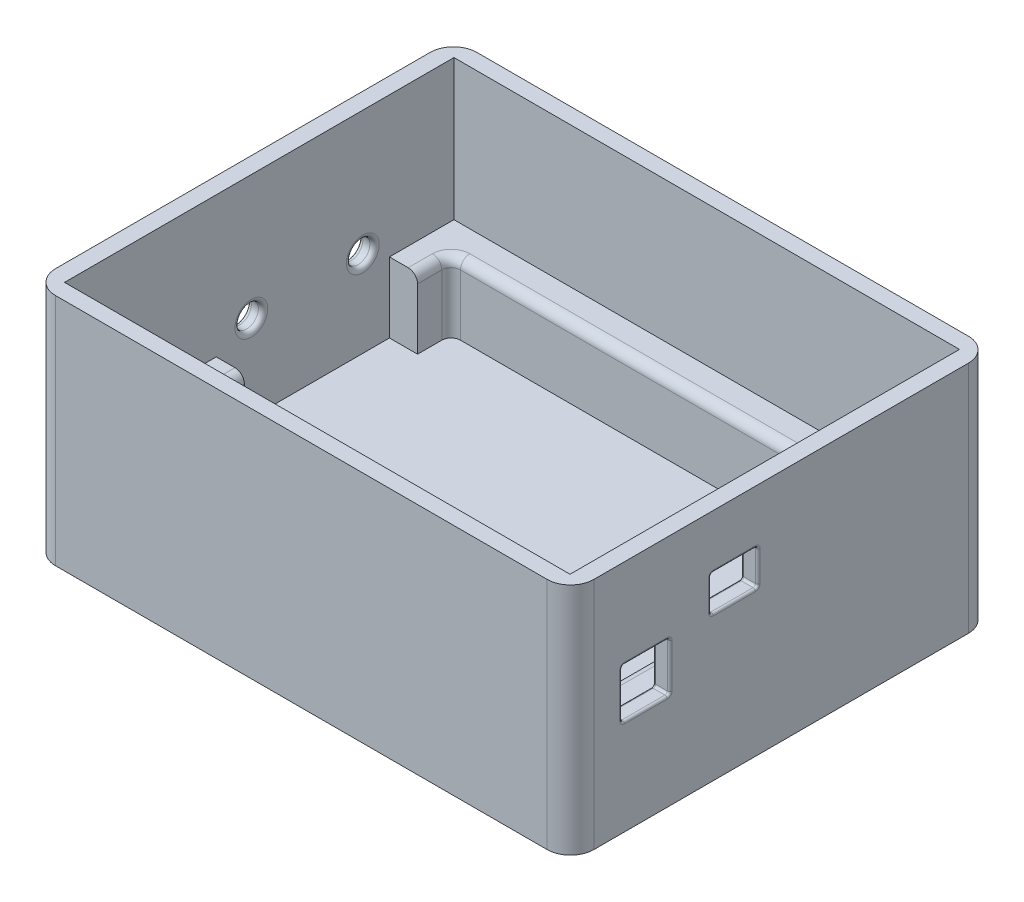
SolidWorks part; units mm, degrees
ref_plane "Front Plane" through (0, 0, 0) normal (0, 0, 1) x (1, 0, 0)
ref_plane "Top Plane" through (0, 0, 0) normal (0, 1, 0) x (1, 0, 0)
ref_plane "Right Plane" through (0, 0, 0) normal (1, 0, 0) x (0, 0, -1)
sketch "Sketch2" plane through (0, 0, 0) normal (0, 1, 0) x (1, 0, 0)
  line L1 (-57.5, 45) -> (57.5, 45)
  line L2 (-57.5, 45) -> (-57.5, -45)
  line L3 (-57.5, -45) -> (57.5, -45)
  line L4 (57.5, 45) -> (57.5, -45)
  line L5 (-57.5, 45) -> (57.5, -45) construction
  line L6 (-57.5, -45) -> (57.5, 45) construction
  point P0 (0, 0)
  dimension "D1" = 115
  dimension "D2" = 90
extrude "Boss-Extrude1" add sketch "Sketch2" along normal blind 50
fillet "Fillet1" radius 5 4 edges at (57.5, 25, 45) (-57.5, 25, 45) (-57.5, 25, -45) (57.5, 25, -45)
sketch "Sketch3" plane through (0, 50, 0) normal (0, 1, 0) x (1, 0, 0)
  line L1 (-54, 41.6) -> (54, 41.6)
  line L2 (-54, 41.6) -> (-54, -41.6)
  line L3 (-54, -41.6) -> (54, -41.6)
  line L4 (54, 41.6) -> (54, -41.6)
  line L5 (-54, 41.6) -> (54, -41.6) construction
  line L6 (-54, -41.6) -> (54, 41.6) construction
  point P0 (0, 0)
  dimension "D1" = 108
  dimension "D2" = 83.2
extrude "Cut-Extrude1" cut sketch "Sketch3" against normal blind 30
sketch "Sketch4" plane through (0, 20, 0) normal (0, 1, 0) x (1, 0, 0)
  line L1 (-48, 35) -> (48, 35)
  line L2 (-48, 35) -> (-48, -35)
  line L3 (-48, -35) -> (48, -35)
  line L4 (48, 35) -> (48, -35)
  line L5 (-48, 35) -> (48, -35) construction
  line L6 (-48, -35) -> (48, 35) construction
  point P0 (0, 0)
  dimension "D1" = 96
  dimension "D2" = 70
extrude "Cut-Extrude2" cut sketch "Sketch4" against normal blind 15
fillet "Fillet2" radius 2 8 edges at (0, 20, 35) (48, 12.5, 35) (-48, 12.5, 35) (-48, 20, 0) (-48, 12.5, -35) (48, 20, 0) (0, 20, -35) (48, 12.5, -35)
sketch "Sketch5" plane through (0, 20, 0) normal (0, 1, 0) x (1, 0, 0)
  line L0 (-54, 41.6) -> (-54, -41.6) construction
  line L1 (-54, 27.8195) -> (-48, 27.8195)
  line L2 (-54, 27.8195) -> (-54, -9.1811)
  line L3 (-54, -9.1811) -> (-48, -9.1811)
  line L4 (-48, 27.8195) -> (-48, -9.1811)
  line L5 (-48, 33) -> (-48, -33) construction
extrude "Cut-Extrude3" cut sketch "Sketch5" against normal blind 15
sketch "Sketch7" plane through (0, 20, 0) normal (0, 1, 0) x (1, 0, 0)
  line L0 (54, -41.6) -> (54, 41.6) construction
  line L1 (54, 33.204) -> (48, 33.204)
  line L2 (54, 33.204) -> (54, 7.8005)
  line L3 (54, 7.8005) -> (48, 7.8005)
  line L4 (48, 33.204) -> (48, 7.8005)
  line L5 (48, -33) -> (48, 33) construction
extrude "Cut-Extrude5" cut sketch "Sketch7" against normal blind 15
sketch "Sketch8" plane through (-54, 0, 0) normal (1, 0, 0) x (0, 0, -1)
  line L0 (41.585, 20.4115) -> (-41.6, 20.4115) construction
  circle A0 centre (22.1259, 23.4115) radius 2.5
  circle A1 centre (-1.6908, 23.4115) radius 2.5
  dimension "D1" = 5
  dimension "D2" = 5
  dimension "D3" = 3
  dimension "D4" = 3
extrude "Cut-Extrude6" cut sketch "Sketch8" against normal blind 10
fillet "Fillet3" radius 1 4 edges at (-57.5, 23.4115, -24.6259) (-57.5, 23.4115, -0.8092) (-54, 23.4115, -0.8092) (-54, 23.4115, -24.6259)
sketch "Sketch9" plane through (54, 0, 0) normal (-1, 0, 0) x (0, 0, 1)
  line L1 (23.82, 30.9115) -> (33.98, 30.9115)
  line L2 (23.82, 30.9115) -> (23.82, 20.5115)
  line L3 (23.82, 20.5115) -> (33.98, 20.5115)
  line L4 (33.98, 30.9115) -> (33.98, 20.5115)
extrude "Cut-Extrude7" cut sketch "Sketch9" against normal blind 10
fillet "Fillet9" radius 0.5 12 edges at (57.5, 25.7115, 33.98) (54, 25.7115, 33.98) (57.5, 30.9115, 28.9) (54, 30.9115, 28.9) (55.75, 30.9115, 33.98) (57.5, 20.5115, 28.9) (55.75, 20.5115, 33.98) (54, 20.5115, 28.9) (57.5, 25.7115, 23.82) (55.75, 20.5115, 23.82) (54, 25.7115, 23.82) (55.75, 30.9115, 23.82)
sketch "Sketch10" plane through (57.5, 0, 0) normal (1, 0, 0) x (0, 0, -1)
  line L0 (-40, 50) -> (-40, 0) construction
  line L1 (-15, 38.4754) -> (-5, 38.4754)
  line L2 (-15, 38.4754) -> (-15, 30.9754)
  line L3 (-15, 30.9754) -> (-5, 30.9754)
  line L4 (-5, 38.4754) -> (-5, 30.9754)
  dimension "D1" = 10
  dimension "D2" = 7.5
  dimension "D3" = 25
extrude "Cut-Extrude8" cut sketch "Sketch10" against normal blind 10
fillet "Fillet10" radius 0.5 12 edges at (54, 38.4754, 10) (57.5, 38.4754, 10) (54, 30.9754, 10) (57.5, 30.9754, 10) (54, 34.7254, 15) (55.75, 30.9754, 15) (57.5, 34.7254, 15) (55.75, 38.4754, 15) (54, 34.7254, 5) (55.75, 38.4754, 5) (57.5, 34.7254, 5) (55.75, 30.9754, 5)
